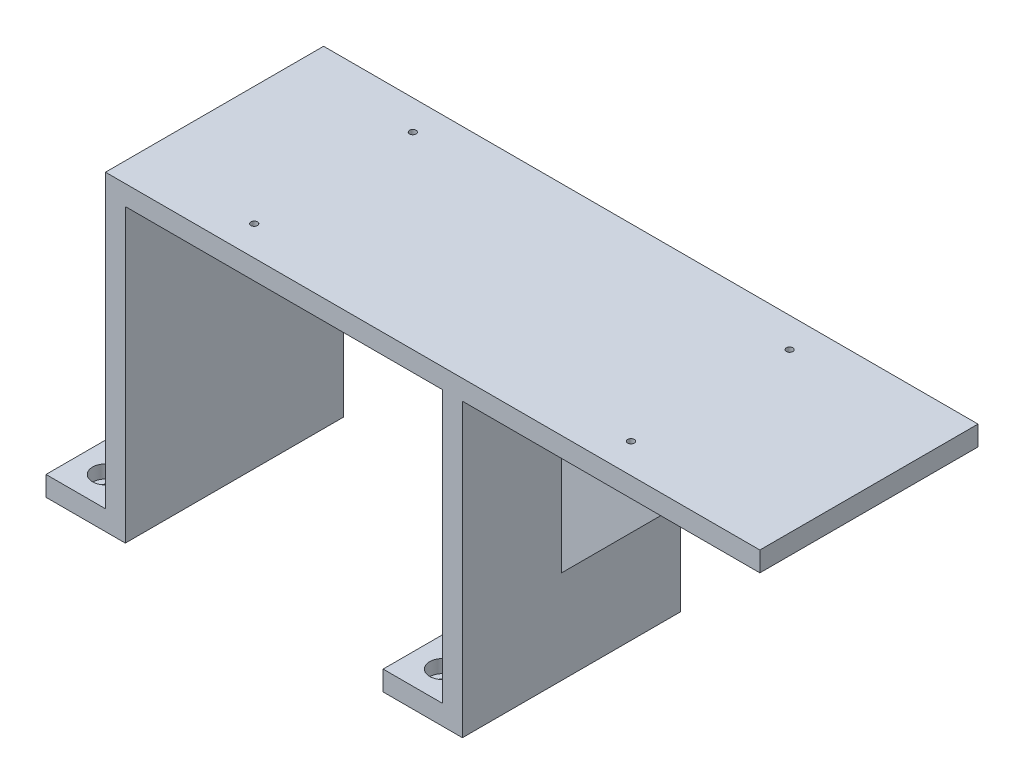
SolidWorks part; units mm, degrees
ref_plane "Front Plane" through (0, 0, 0) normal (0, 0, 1) x (1, 0, 0)
ref_plane "Top Plane" through (0, 0, 0) normal (0, 1, 0) x (1, 0, 0)
ref_plane "Right Plane" through (0, 0, 0) normal (1, 0, 0) x (0, 0, -1)
sketch "Sketch1" plane through (0, 0, 0) normal (0, 0, 1) x (1, 0, 0)
  line L0 (0, 0) -> (30, 0)
  line L1 (30, 0) -> (30, 147)
  line L2 (30, 147) -> (210, 147)
  line L3 (210, 147) -> (210, -10)
  line L5 (0, 0) -> (0, -10)
  line L6 (0, -10) -> (40, -10)
  line L7 (40, -10) -> (40, 137)
  line L8 (40, 137) -> (200, 137)
  line L9 (200, 137) -> (200, 0)
  line L10 (170, -10) -> (170, 0)
  line L11 (170, 0) -> (200, 0)
  line L12 (210, -10) -> (170, -10)
  dimension "D1" = 157
  dimension "D2" = 10
  dimension "D3" = 10
  dimension "D4" = 30
  dimension "D5" = 10
  dimension "D6" = 10
  dimension "D7" = 30
  dimension "D8" = 160
extrude "Boss-Extrude1" add sketch "Sketch1" along normal blind 110
sketch "Sketch2" plane through (0, 0, 0) normal (0, 1, 0) x (1, 0, 0)
  line L0 (30, -110) -> (0, -110) construction
  line L2 (200, -110) -> (170, -110) construction
  line L3 (30, 0) -> (0, 0) construction
  circle A0 centre (15, -15) radius 3.3
  circle A1 centre (15, -95) radius 3.3
  circle A2 centre (185, -95) radius 3.3
  circle A3 centre (185, -15) radius 3.3
  point P11 (15, -110)
  point P14 (185, -110)
  dimension "D3" = 6.6
  dimension "D1" = 15
  dimension "D2" = 15
extrude "Cut-Extrude1" cut sketch "Sketch2" against normal through all
sketch "Sketch3" plane through (0, 0, 0) normal (0, 1, 0) x (1, 0, 0)
  circle A0 centre (15, -15) radius 6.5
  circle A1 centre (15, -95) radius 6.5
  circle A2 centre (185, -95) radius 6.5
  circle A3 centre (185, -15) radius 6.5
  dimension "D1" = 13
extrude "Cut-Extrude2" cut sketch "Sketch3" against normal blind 6.6
sketch "Sketch5" plane through (0, 0, 110) normal (0, 0, 1) x (1, 0, 0)
  line L0 (210, 147) -> (30, 147) construction
  line L1 (210, 147) -> (360, 147)
  line L2 (210, 147) -> (210, 137)
  line L3 (210, 137) -> (360, 137)
  line L4 (360, 147) -> (360, 137)
  dimension "D1" = 10
  dimension "D2" = 150
extrude "Boss-Extrude2" add sketch "Sketch5" against normal up to vertex (110 mm away)
ref_plane "Plane1" through (0, 0, 55) normal (0, 0, 1) x (1, 0, 0)
sketch "Sketch6" plane through (0, 0, 55) normal (0, 0, 1) x (1, 0, 0)
  line L0 (210, 37) -> (310, 137)
  line L1 (210, -10) -> (210, 137) construction
  line L2 (210, 137) -> (360, 137) construction
  line L3 (310, 137) -> (210, 137)
  line L4 (210, 137) -> (210, 37)
  dimension "D1" = 100
  dimension "D2" = 100
extrude "Boss-Extrude3" add sketch "Sketch6" along normal mid plane 10
sketch "Sketch4" plane through (0, 147, 0) normal (0, 1, 0) x (1, 0, 0)
  line L0 (90, -15) -> (90, -95) construction
  line L1 (30, -110) -> (30, 0) construction
  point P4 (30, -55)
  point P5 (90, -55)
  point P13 (90, -15)
  point P14 (90, -95)
  point P15 (280, -95)
  point P16 (280, -15)
  dimension "D1" = 80
  dimension "D2" = 60
hole_wizard "M4 Tapped Hole1" positions "Sketch7" profile "Sketch8" tap size "M4" standard "ISO" end condition through all
sketch "Sketch7" plane through (0, 147, 0) normal (0, 1, 0) x (1, 0, 0)
  point P0 (90, -15)
  point P3 (280, -15)
  point P6 (280, -95)
  point P9 (90, -95)
cosmetic thread "Hole Thread1" parameters "D2"=4
cosmetic thread "Hole Thread2" parameters "D2"=4
cosmetic thread "Hole Thread3" parameters "D2"=4
cosmetic thread "Hole Thread4" parameters "D2"=4
sketch "Sketch8" plane through (90, 147, 15) normal (1, 0, 0) x (0, 0, 1)
  line L0 (0, 0) -> (0, 157)
  line L1 (0, 157) -> (1.65, 157)
  line L2 (1.65, 157) -> (1.65, 0)
  line L5 (1.65, 0) -> (0, 0)
  line L11 (0, -6.35) -> (0, 107.95) construction
  dimension "Thru Tap Drill Dia." = 3.3
  dimension "Thru Tap Drill Depth" = 157
